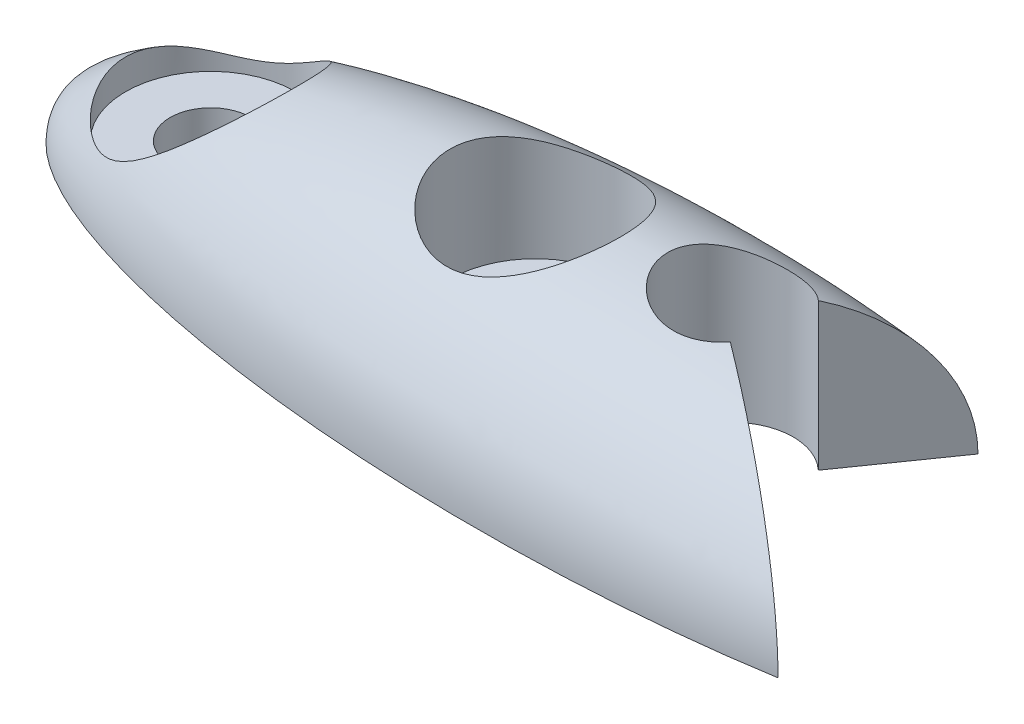
SolidWorks part; units mm, degrees
ref_plane "Front Plane" through (0, 0, 0) normal (0, 0, 1) x (1, 0, 0)
ref_plane "Top Plane" through (0, 0, 0) normal (0, 1, 0) x (1, 0, 0)
ref_plane "Right Plane" through (0, 0, 0) normal (1, 0, 0) x (0, 0, -1)
sketch "Sketch1" plane through (0, 0, 0) normal (0, 0, 1) x (1, 0, 0)
  line L0 (-14, 0) -> (14, 0) construction
  line L1 (-14, 0) -> (14, 0)
  circle A0 centre (-10.75, 0) radius 1 construction
  circle A1 centre (10.75, 0) radius 1 construction
  ellipse E0 centre (0, 0) end of major axis (14, 0) minor radius 4 (14, 0) -> (-14, 0) ccw
  dimension "D3" = 2
  dimension "D1" = 14
  dimension "D2" = 4
  dimension "D4" = 3.25
  dimension "D5" = 3.25
revolve "Revolve1" add sketch "Sketch1" angle 360 about L0
sketch "Sketch2" plane through (0, 0, 0) normal (0, 0, 1) x (1, 0, 0)
  line L1 (-26.9158, 0) -> (23.719, 0)
  line L2 (-26.9158, 0) -> (-26.9158, -13.0728)
  line L3 (-26.9158, -13.0728) -> (23.719, -13.0728)
  line L4 (23.719, 0) -> (23.719, -13.0728)
extrude "Cut-Extrude1" cut sketch "Sketch2" against normal through all both and the other way through all
sketch "Sketch3" plane through (0, 0, 0) normal (0, -1, 0) x (1, 0, 0)
  line L0 (-14, 0) -> (14, 0) construction
  circle A0 centre (-10.5, 0) radius 1
  circle A1 centre (-2.5, 0) radius 1
  ellipse E0 centre (0, 0) end of major axis (14, 0) minor radius 4 (-14, 0) -> (14, 0) ccw construction
  ellipse E1 centre (0, 0) end of major axis (14, 0) minor radius 4 (14, 0) -> (-14, 0) ccw construction
  dimension "D1" = 2
  dimension "D2" = 3.5
  dimension "D3" = 8
extrude "Cut-Extrude2" cut sketch "Sketch3" against normal through all
ref_plane "Plane1" through (0, 1, 0) normal (0, -1, 0) x (-1, 0, 0)
sketch "Sketch4" plane through (0, 1, 0) normal (0, -1, 0) x (-1, 0, 0)
  circle A0 centre (10.5, 0) radius 2.1
  circle A1 centre (2.5, 0) radius 2.1
  dimension "D1" = 4.2
extrude "Cut-Extrude3" cut sketch "Sketch4" against normal through all
sketch "Sketch5" plane through (0, 0, 0) normal (0, -1, 0) x (1, 0, 0)
  line L0 (-14, 0) -> (14, 0) construction
  circle A0 centre (2, -0.36) radius 1.5
  circle A1 centre (-2.5, 0) radius 1 construction
  ellipse E0 centre (0, 0) end of major axis (14, 0) minor radius 4 (-14, 0) -> (14, 0) ccw construction
  point P14 (2, -0.5829)
  dimension "D1" = 4.5
  dimension "D3" = 3
  dimension "D2" = 0.36
extrude "Cut-Extrude4" cut sketch "Sketch5" against normal through all
sketch "Sketch6" plane through (0, 0, 0) normal (0, -1, 0) x (1, 0, 0)
  line L0 (-14, 0) -> (14, 0) construction
  line L1 (6.9573, 3.4711) -> (2, 0)
  line L2 (2, 0) -> (4.6424, -3.7737)
  ellipse E0 centre (0, 0) end of major axis (14, 0) minor radius 4 (14, 0) -> (-14, 0) ccw construction
  ellipse E1 centre (0, 0) end of major axis (14, 0) minor radius 4 (-14, 0) -> (14, 0) ccw construction
  ellipse E2 centre (0, 0) end of major axis (14, 0) minor radius 4 (14, 0) -> (6.9573, 3.4711) ccw
  ellipse E3 centre (0, 0) end of major axis (14, 0) minor radius 4 (4.6424, -3.7737) -> (14, 0) ccw
  ellipse M7 centre (0, 0) end of major axis (14, 0) minor radius 4 (14, 0) -> (-14, 0) ccw
  ellipse M8 centre (0, 0) end of major axis (14, 0) minor radius 4 (-14, 0) -> (14, 0) ccw
  dimension "D1" = 55
  dimension "D2" = 12
extrude "Cut-Extrude5" cut sketch "Sketch6" against normal through all both and the other way through all contours L1 L0 M7 | L0 L2 M8
